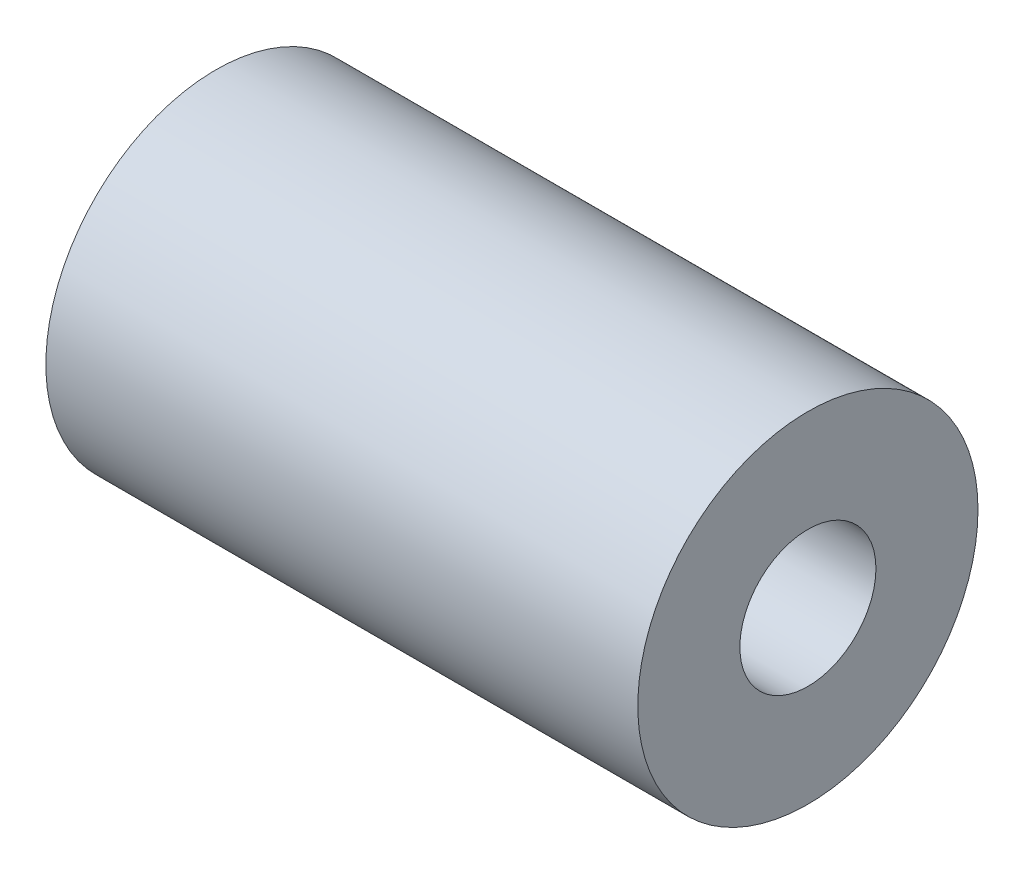
SolidWorks part; units mm, degrees
material "KNSB95"
ref_plane "Plano frontal" through (0, 0, 0) normal (0, 0, 1) x (1, 0, 0)
ref_plane "Plano superior" through (0, 0, 0) normal (0, 1, 0) x (1, 0, 0)
ref_plane "Plano direito" through (0, 0, 0) normal (1, 0, 0) x (0, 0, -1)
sketch "Esboço1" plane through (0, 0, 0) normal (0, 0, 1) x (1, 0, 0)
  line L0 (0, 0) -> (-38391.3191, 0) construction
  line L1 (0, -767.8264) -> (0, 37623.4927) construction
  line L3 (0, 25) -> (87, 25)
  line L4 (0, 25) -> (0, 10)
  line L5 (0, 10) -> (87, 10)
  line L6 (87, 25) -> (87, 10)
  dimension "D1" = 87
  dimension "D2" = 25
  dimension "D3" = 10
revolve "Revolução1" add sketch "Esboço1" angle 360 about L0
equation "\"D2@Esboço1\"=25"
